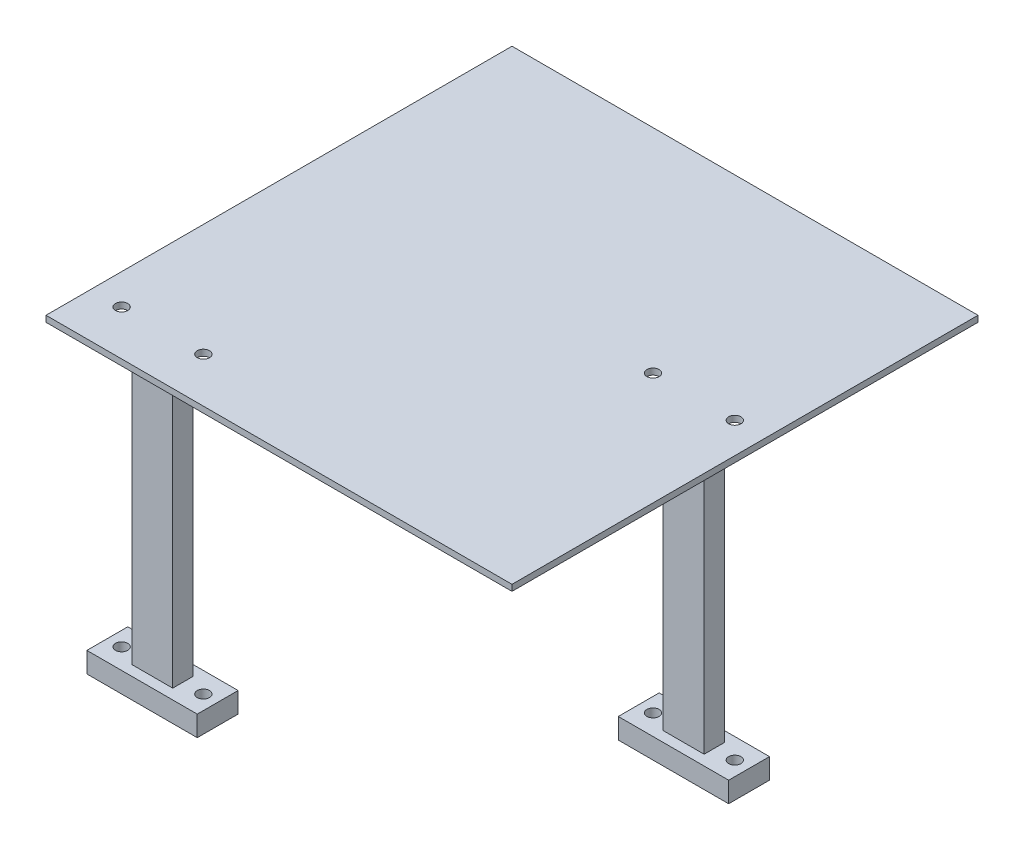
SolidWorks part; units mm, degrees
material "ABS"
ref_plane "Front Plane" through (0, 0, 0) normal (0, 0, 1) x (1, 0, 0)
ref_plane "Top Plane" through (0, 0, 0) normal (0, 1, 0) x (1, 0, 0)
ref_plane "Right Plane" through (0, 0, 0) normal (1, 0, 0) x (0, 0, -1)
sketch "Sketch1" plane through (0, 0, 0) normal (0, 1, 0) x (1, 0, 0)
  line L0 (-57, 57) -> (-57, -57)
  line L1 (-60, 60) -> (60, 60) construction
  line L2 (-60, 60) -> (-60, -60) construction
  line L3 (-60, -60) -> (60, -60) construction
  line L4 (60, 60) -> (60, -60) construction
  line L5 (-60, 60) -> (60, -60) construction
  line L6 (-60, -60) -> (60, 60) construction
  line L7 (-57, -57) -> (57, -57)
  line L8 (57, 57) -> (57, -57)
  line L9 (-57, 57) -> (57, 57)
  line L10 (-49.5, -46) -> (-29.5, -46) construction
  line L11 (29.5, 5) -> (49.5, 5) construction
  circle A0 centre (29.5, 5) radius 1.5
  circle A1 centre (49.5, 5) radius 1.5
  circle A2 centre (-29.5, -46) radius 1.5
  circle A4 centre (-49.5, -46) radius 1.5
  point P0 (0, 0)
  point P13 (-39.5, -46)
  point P16 (39.5, 5)
  dimension "D9" = 3
  dimension "D1" = 120
  dimension "D2" = 120
  dimension "D4" = 20.5
  dimension "D5" = 20
  dimension "D6" = 14
  dimension "D7" = 55
  dimension "D8" = 20.5
  dimension "D3" = 3
extrude "Boss-Extrude1" add sketch "Sketch1" along normal blind 1.5
sketch "Sketch2" plane through (0, 1.5, 0) normal (0, 1, 0) x (1, 0, 0)
  line L0 (-49.5, -46) -> (-29.5, -46) construction
  line L1 (29.5, 5) -> (49.5, 5) construction
  line L3 (-44.5, -43.5) -> (-34.5, -43.5)
  line L4 (-44.5, -43.5) -> (-44.5, -48.5)
  line L5 (-44.5, -48.5) -> (-34.5, -48.5)
  line L6 (-34.5, -43.5) -> (-34.5, -48.5)
  line L7 (-44.5, -43.5) -> (-34.5, -48.5) construction
  line L8 (-44.5, -48.5) -> (-34.5, -43.5) construction
  line L9 (34.5, 7.5) -> (44.5, 7.5)
  line L10 (34.5, 7.5) -> (34.5, 2.5)
  line L11 (34.5, 2.5) -> (44.5, 2.5)
  line L12 (44.5, 7.5) -> (44.5, 2.5)
  line L13 (34.5, 7.5) -> (44.5, 2.5) construction
  line L14 (34.5, 2.5) -> (44.5, 7.5) construction
  point P8 (-39.5, -46)
  point P13 (39.5, 5)
  dimension "D1" = 10
  dimension "D2" = 5
extrude "Boss-Extrude2" add sketch "Sketch2" against normal blind 72
sketch "Sketch3" plane through (0, -70.5, 0) normal (0, -1, 0) x (-1, 0, 0)
  line L0 (49.5, -46) -> (29.5, -46) construction
  line L1 (-29.5, 5) -> (-49.5, 5) construction
  line L2 (26, -41) -> (53, -41)
  line L3 (26, -41) -> (26, -51)
  line L4 (26, -51) -> (53, -51)
  line L5 (53, -41) -> (53, -51)
  line L6 (26, -41) -> (53, -51) construction
  line L7 (26, -51) -> (53, -41) construction
  line L9 (-53, 10) -> (-26, 10)
  line L10 (-53, 10) -> (-53, 0)
  line L11 (-53, 0) -> (-26, 0)
  line L12 (-26, 10) -> (-26, 0)
  line L13 (-53, 10) -> (-26, 0) construction
  line L14 (-53, 0) -> (-26, 10) construction
  circle A0 centre (49.5, -46) radius 1.5
  circle A1 centre (29.5, -46) radius 1.5
  circle A2 centre (-29.5, 5) radius 1.5
  circle A3 centre (-49.5, 5) radius 1.5
  point P4 (39.5, -46)
  point P15 (-39.5, 5)
  dimension "D3" = 3
  dimension "D1" = 27
  dimension "D2" = 10
extrude "Boss-Extrude3" add sketch "Sketch3" along normal blind 5
